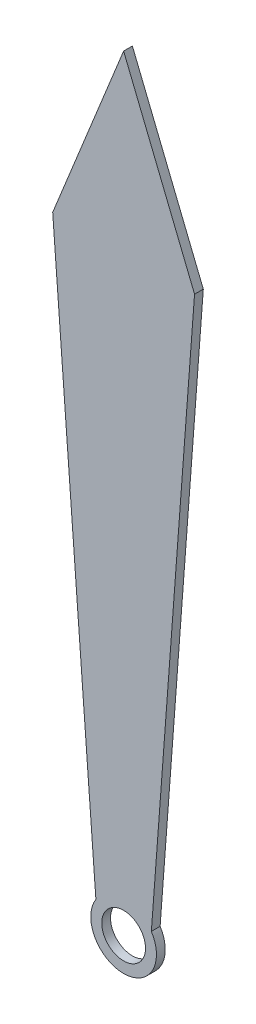
SolidWorks part; units mm, degrees
ref_plane "Alzado" through (0, 0, 0) normal (0, 0, 1) x (1, 0, 0)
ref_plane "Planta" through (0, 0, 0) normal (0, 1, 0) x (1, 0, 0)
ref_plane "Vista lateral" through (0, 0, 0) normal (1, 0, 0) x (0, 0, -1)
sketch "Croquis1" plane through (0, 0, 0) normal (0, 0, 1) x (1, 0, 0)
  line L0 (0, 0) -> (0, 17.5) construction
  line L1 (-0.6336, 0.4013) -> (-1.6202, 13.5)
  line L2 (-1.6202, 13.5) -> (0, 17.5)
  line L3 (0.6336, 0.4013) -> (1.6202, 13.5)
  line L4 (1.6202, 13.5) -> (0, 17.5)
  circle A0 centre (0, 0) radius 0.5
  circle A1 centre (0, 0) radius 0.75
  dimension "D2" = 1
  dimension "D3" = 1.5
  dimension "D1" = 17.5
  dimension "D4" = 4
extrude "Saliente-Extruir2" add sketch "Croquis1" along normal blind 0.2
